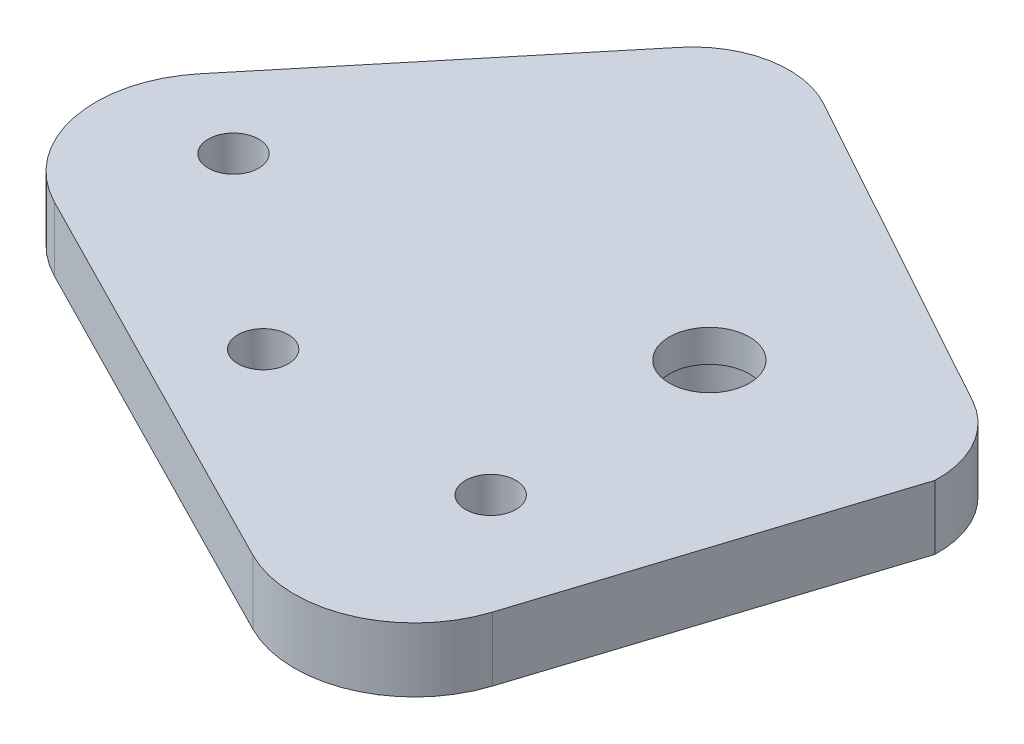
SolidWorks part; units mm, degrees
ref_plane "Front Plane" through (0, 0, 0) normal (0, 0, 1) x (1, 0, 0)
ref_plane "Top Plane" through (0, 0, 0) normal (0, 1, 0) x (1, 0, 0)
ref_plane "Right Plane" through (0, 0, 0) normal (1, 0, 0) x (0, 0, -1)
sketch "Sketch1" plane through (0, 0, 0) normal (0, 1, 0) x (1, 0, 0)
  line L9 (-36.0642, 30.1982) -> (-36.0642, 45.0551)
  line L11 (5.0242, -12.5754) -> (57.86, 4.654)
  line L13 (57.86, 4.654) -> (63.1927, 49.9788)
  line L14 (63.1927, 49.9788) -> (25.9283, 75.0284)
  line L15 (25.9283, 75.0284) -> (-24.4562, 60.5082)
  line L18 (-26.7937, -0.9344) -> (-36.0642, 30.1982)
  line L19 (-36.0642, 45.0551) -> (-24.4562, 60.5082)
  line L23 (5.0242, -12.5754) -> (-26.7937, -0.9344)
extrude "Boss-Extrude2" add sketch "Sketch1" along normal blind 8
sketch "Sketch2" plane through (0, 8, 0) normal (0, 1, 0) x (1, 0, 0)
  line L0 (-0.9926, 5.0237) -> (-23.9739, 24.3073)
  circle A0 centre (-0.9926, 5.0237) radius 3.15
  circle A1 centre (-23.9739, 24.3073) radius 3.15
sketch "Sketch7" plane through (0, 8, 0) normal (0, 1, 0) x (1, 0, 0)
  line L0 (-40.8206, 23.4296) -> (-5.3719, -12.0191)
  line L1 (-40.8206, 23.4296) -> (-8.1976, 82.9275)
  line L2 (-8.1976, 82.9275) -> (73.0578, 41.0836)
  line L3 (73.0578, 41.0836) -> (42.9406, -17.4001)
  line L4 (42.9406, -17.4001) -> (-5.3719, -12.0191)
  line L5 (-23.9008, 101.0328) -> (-57.9014, 20.737)
  line L6 (-57.9014, 20.737) -> (-18.159, -32.5338)
  line L7 (-18.159, -32.5338) -> (87.9242, -9.9612)
  line L8 (87.9242, -9.9612) -> (85.312, 49.3156)
  line L9 (85.312, 49.3156) -> (-23.9008, 101.0328)
extrude "Cut-Extrude5" cut sketch "Sketch7" against normal blind 18.5
sketch "Sketch8" plane through (0, 8, 0) normal (0, 1, 0) x (1, 0, 0)
  line L0 (-8.1976, 82.9275) -> (-40.8206, 23.4296)
  line L1 (-40.8206, 23.4296) -> (-5.3719, -12.0191)
  line L2 (-5.3719, -12.0191) -> (42.9406, -17.4001)
  line L3 (42.9406, -17.4001) -> (73.0578, 41.0836)
  line L4 (73.0578, 41.0836) -> (-8.1976, 82.9275)
  line L5 (7.4196, 62.0055) -> (-9.7469, 64.7472)
  line L6 (13.8825, 71.557) -> (-19.7459, 61.8657) construction
  line L7 (-9.7469, 64.7472) -> (-32.4016, 23.4296)
  line L8 (-32.4016, 23.4296) -> (0, -4.6748)
  line L9 (0, -4.6748) -> (46.1975, 11.8418)
  line L10 (46.1975, 11.8418) -> (56.0255, 35.9436)
  line L11 (56.0255, 35.9436) -> (7.4196, 62.0055)
extrude "Boss-Extrude7" add sketch "Sketch8" against normal blind 8
sketch "Sketch9" plane through (0, 0, 0) normal (0, -1, 0) x (-1, 0, 0)
  circle A0 centre (-28.9418, 3.4739) radius 3.15
extrude "Cut-Extrude6" cut sketch "Sketch9" against normal blind 8
sketch "Sketch10" plane through (0, 8, 0) normal (0, 1, 0) x (1, 0, 0)
  line L0 (-33.8726, 31.8418) -> (-7.6109, 63.6375)
  line L1 (7.4316, 66.5062) -> (48.8705, 43.6771)
  line L3 (42.9406, -17.4001) -> (73.0578, 41.0836) construction
  line L6 (-40.8206, 23.4296) -> (-5.3719, -12.0191) construction
  line L8 (-51.0279, 26.4997) -> (-18.338, 89.9793)
  line L9 (-18.338, 89.9793) -> (70.6189, 64.73)
  line L10 (70.6189, 64.73) -> (85.8622, 8.3294)
  line L11 (85.8622, 8.3294) -> (41.1982, -31.6467)
  line L12 (41.1982, -31.6467) -> (-23.676, -9.8144)
  line L13 (-23.676, -9.8144) -> (-51.0279, 26.4997)
  line L14 (55.073, 32.7548) -> (41.7063, -9.0649)
  line L15 (-33.8726, 31.8418) -> (-34.7005, 30.8395)
  line L16 (-29.9508, 7.925) -> (20.6029, -17.8603)
  arc A2 (55.073, 32.7548) -> (48.8705, 43.6771) centre (43.0801, 33.1665) ccw
  arc A3 (7.4316, 66.5062) -> (-7.6109, 63.6375) centre (1.6412, 55.9956) ccw
  arc A7 (41.7063, -9.0649) -> (20.6029, -17.8603) centre (27.4184, -4.4981) cw
  arc A8 (-29.9508, 7.925) -> (-34.7005, 30.8395) centre (-23.1353, 21.2872) cw
  point P20 (-9.3641, -8.0269)
  point P23 (54.0948, 4.26)
  point P30 (42.9406, -17.4001)
  point P33 (-40.8206, 23.4296)
  dimension "D1" = 15
extrude "Cut-Extrude8" cut sketch "Sketch10" against normal blind 8
sketch "Sketch12" plane through (0, 8, 0) normal (0, 1, 0) x (1, 0, 0)
  line L0 (-34.7005, 30.8395) -> (-23.7994, 10.8786)
  line L1 (-23.7994, 10.8786) -> (16.2733, -10.7751)
  line L2 (16.2733, -10.7751) -> (41.7063, -9.0649)
  line L3 (-29.9508, 7.925) -> (20.6029, -17.8603)
  arc A0 (-34.7005, 30.8395) -> (-29.9508, 7.925) centre (-23.1353, 21.2872) ccw
  arc A1 (20.6029, -17.8603) -> (41.7063, -9.0649) centre (27.4184, -4.4981) ccw
extrude "Boss-Extrude8" add sketch "Sketch12" against normal blind 8
sketch "Sketch14" plane through (0, 0, 0) normal (0, -1, 0) x (-1, 0, 0)
  line L0 (-28.0063, 31.6875) -> (-28.9418, 3.4739)
  circle A0 centre (-28.0063, 31.6875) radius 5
extrude "Cut-Extrude10" cut sketch "Sketch14" against normal blind 10
sketch "Sketch15" plane through (0, 0, 0) normal (0, -1, 0) x (1, 0, 0)
  circle A0 centre (28.0063, -31.6875) radius 6
extrude "Cut-Extrude11" cut sketch "Sketch15" against normal blind 4
extrude "Cut-Extrude12" cut sketch "Sketch2" against normal blind 48
